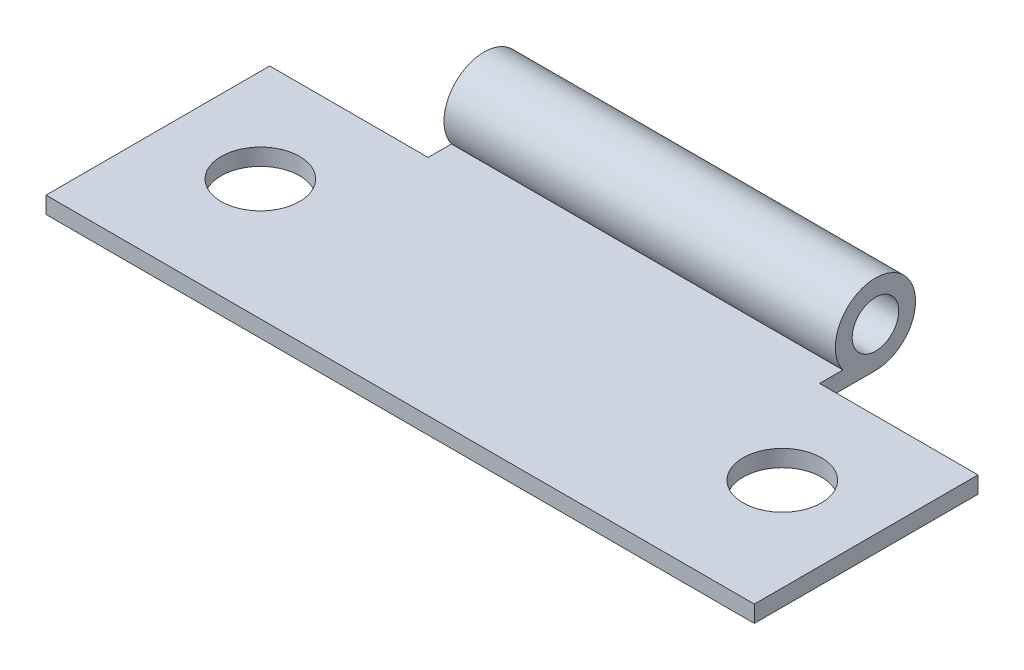
SolidWorks part; units mm, degrees
ref_plane "前视基准面" through (0, 0, 0) normal (0, 0, 1) x (1, 0, 0)
ref_plane "上视基准面" through (0, 0, 0) normal (0, 1, 0) x (1, 0, 0)
ref_plane "右视基准面" through (0, 0, 0) normal (1, 0, 0) x (0, 0, -1)
sketch "草图1" plane through (0, 0, 0) normal (1, 0, 0) x (0, 0, -1)
  line L0 (0, -2.15) -> (-15, -2.15)
  line L1 (-15, -2.15) -> (-15, -1.25)
  line L2 (-1.7493, -1.25) -> (-15, -1.25)
  circle A0 centre (0, 0) radius 1.25
  arc A1 (0, -2.15) -> (-1.7493, -1.25) centre (0, 0) ccw
  dimension "D1" = 4.3
  dimension "D2" = 0.9
  dimension "D3" = 15
extrude "凸台-拉伸1" add sketch "草图1" along normal blind 38
sketch "草图2" plane through (0, 0, 0) normal (0, 1, 0) x (1, 0, 0)
  line L0 (19, 6.6145) -> (19, -19.2902) construction
  line L1 (0, -1.7493) -> (0, -15) construction
  line L2 (38, -1.7493) -> (38, -15) construction
  line L3 (38, -15) -> (0, -15) construction
  line L8 (29.5, 5.8901) -> (29.5, -3)
  line L9 (0, 5.8901) -> (8.5, 5.8901)
  line L10 (0, 5.8901) -> (0, -3)
  line L11 (0, -3) -> (8.5, -3)
  line L12 (8.5, 5.8901) -> (8.5, -3)
  line L13 (38, -3) -> (29.5, -3)
  line L14 (38, 5.8901) -> (38, -3)
  line L15 (38, 5.8901) -> (29.5, 5.8901)
  circle A0 centre (33, -8.5) radius 2.1
  circle A1 centre (5, -8.5) radius 2.1
  dimension "D3" = 8.5
  dimension "D4" = 4.2
  dimension "D5" = 28
  dimension "D1" = 12
  dimension "D2" = 8.5
extrude "切除-拉伸1" cut sketch "草图2" against normal mid plane 38
